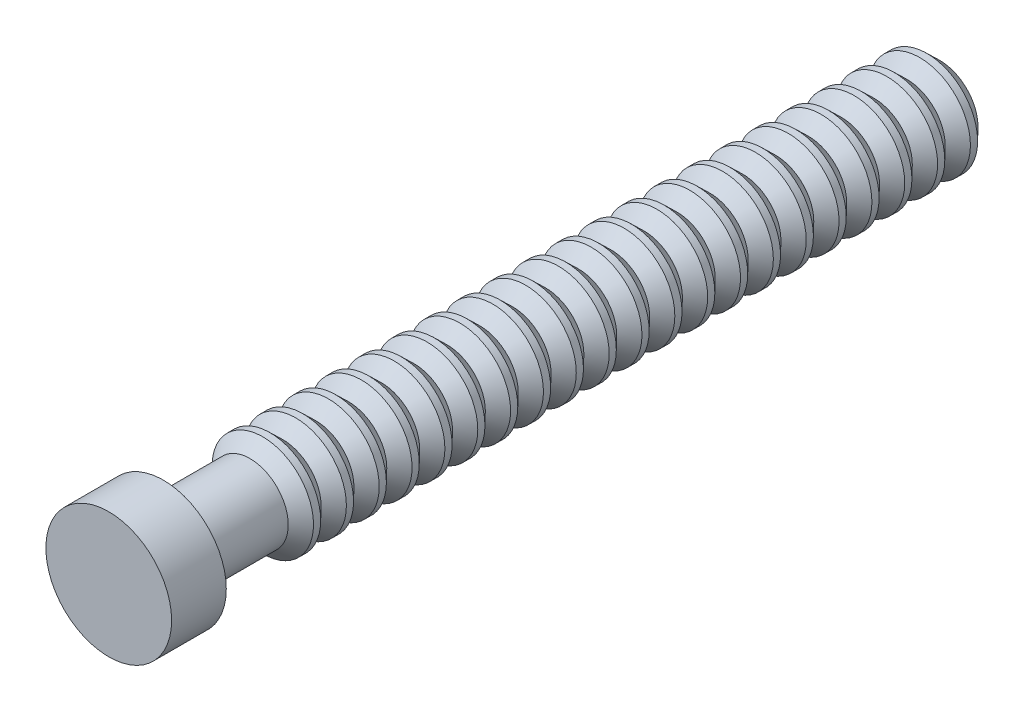
SolidWorks part; units mm, degrees
material "ASTM A36 Steel"
ref_plane "Front Plane" through (0, 0, 0) normal (0, 0, 1) x (1, 0, 0)
ref_plane "Top Plane" through (0, 0, 0) normal (0, 1, 0) x (1, 0, 0)
ref_plane "Right Plane" through (0, 0, 0) normal (1, 0, 0) x (0, 0, -1)
sketch "Sketch1" plane through (0, 0, 0) normal (0, 0, 1) x (1, 0, 0)
  circle A0 centre (0, 0) radius 7.3025
  dimension "D1" = 14.605
extrude "Boss-Extrude1" add sketch "Sketch1" along normal blind 6.35
sketch "Sketch2" plane through (0, 0, 0) normal (0, 0, 1) x (1, 0, 0)
  circle A0 centre (0, 0) radius 4.445
  dimension "D1" = 8.89
extrude "Boss-Extrude2" add sketch "Sketch2" against normal blind 90.17
sketch "Sketch5" plane through (0, 0, 0) normal (1, 0, 0) x (0, 0, -1)
  line L0 (90.17, 0) -> (99.2048, 0) construction
  line L1 (90.17, -4.445) -> (90.17, 4.445) construction
sketch "Sketch7" plane through (0, 0, 0) normal (1, 0, 0) x (0, 0, -1)
  line L0 (6.3474, 4.4475) -> (6.3449, 4.445)
  line L2 (86.3574, 4.4475) -> (84.8678, 5.8902)
  line L4 (86.36, 4.445) -> (84.8678, 5.8902)
  line L45 (84.8678, 5.8902) -> (84.0342, 5.8902)
  line L46 (84.0342, 5.8902) -> (82.5474, 4.4475)
  line L47 (82.5474, 4.4475) -> (81.0578, 5.8902)
  line L48 (90.17, 4.445) -> (88.6778, 5.8902)
  line L49 (88.6778, 5.8902) -> (87.8442, 5.8902)
  line L50 (87.8442, 5.8902) -> (86.3574, 4.4475)
  line L51 (82.5474, 4.4475) -> (81.0578, 5.8902)
  line L52 (90.17, 4.445) -> (0, 4.445) construction
  line L53 (81.0578, 5.8902) -> (80.2242, 5.8902)
  line L54 (6.3449, 4.445) -> (6.35, 4.445)
  line L55 (86.36, 4.445) -> (90.17, 4.445)
  line L56 (80.2242, 5.8902) -> (78.7374, 4.4475)
  line L57 (74.93, 4.445) -> (86.36, 4.445)
  line L59 (78.7374, 4.4475) -> (77.2478, 5.8902)
  line L62 (78.7374, 4.4475) -> (77.2478, 5.8902)
  line L65 (77.2478, 5.8902) -> (76.4142, 5.8902)
  line L68 (76.4142, 5.8902) -> (74.9274, 4.4475)
  line L71 (74.9274, 4.4475) -> (73.4378, 5.8902)
  line L74 (74.9274, 4.4475) -> (73.4378, 5.8902)
  line L77 (73.4378, 5.8902) -> (72.6042, 5.8902)
  line L80 (72.6042, 5.8902) -> (71.1174, 4.4475)
  line L83 (71.1174, 4.4475) -> (69.6278, 5.8902)
  line L86 (71.1174, 4.4475) -> (69.6278, 5.8902)
  line L89 (69.6278, 5.8902) -> (68.7942, 5.8902)
  line L92 (68.7942, 5.8902) -> (67.3074, 4.4475)
  line L95 (67.3074, 4.4475) -> (65.8178, 5.8902)
  line L98 (67.3074, 4.4475) -> (65.8178, 5.8902)
  line L101 (65.8178, 5.8902) -> (64.9842, 5.8902)
  line L104 (64.9842, 5.8902) -> (63.4974, 4.4475)
  line L107 (63.4974, 4.4475) -> (62.0078, 5.8902)
  line L110 (63.4974, 4.4475) -> (62.0078, 5.8902)
  line L111 (62.0078, 5.8902) -> (61.1742, 5.8902)
  line L113 (61.1742, 5.8902) -> (59.6874, 4.4475)
  line L114 (59.6874, 4.4475) -> (58.1978, 5.8902)
  line L115 (59.6874, 4.4475) -> (58.1978, 5.8902)
  line L116 (58.1978, 5.8902) -> (57.3642, 5.8902)
  line L117 (57.3642, 5.8902) -> (55.8774, 4.4475)
  line L118 (55.8774, 4.4475) -> (54.3878, 5.8902)
  line L119 (55.8774, 4.4475) -> (54.3878, 5.8902)
  line L120 (54.3878, 5.8902) -> (53.5542, 5.8902)
  line L121 (53.5542, 5.8902) -> (52.0674, 4.4475)
  line L122 (52.0674, 4.4475) -> (50.5778, 5.8902)
  line L123 (52.0674, 4.4475) -> (50.5778, 5.8902)
  line L124 (50.5778, 5.8902) -> (49.7442, 5.8902)
  line L125 (49.7442, 5.8902) -> (48.2574, 4.4475)
  line L126 (48.2574, 4.4475) -> (46.7678, 5.8902)
  line L127 (48.2574, 4.4475) -> (46.7678, 5.8902)
  line L128 (46.7678, 5.8902) -> (45.9342, 5.8902)
  line L129 (45.9342, 5.8902) -> (44.4474, 4.4475)
  line L130 (44.4474, 4.4475) -> (42.9578, 5.8902)
  line L131 (44.4474, 4.4475) -> (42.9578, 5.8902)
  line L132 (42.9578, 5.8902) -> (42.1242, 5.8902)
  line L133 (42.1242, 5.8902) -> (40.6374, 4.4475)
  line L134 (40.6374, 4.4475) -> (39.1478, 5.8902)
  line L135 (40.6374, 4.4475) -> (39.1478, 5.8902)
  line L136 (39.1478, 5.8902) -> (38.3142, 5.8902)
  line L137 (38.3142, 5.8902) -> (36.8274, 4.4475)
  line L138 (36.8274, 4.4475) -> (35.3378, 5.8902)
  line L139 (36.8274, 4.4475) -> (35.3378, 5.8902)
  line L140 (35.3378, 5.8902) -> (34.5042, 5.8902)
  line L141 (34.5042, 5.8902) -> (33.0174, 4.4475)
  line L142 (33.0174, 4.4475) -> (31.5278, 5.8902)
  line L143 (33.0174, 4.4475) -> (31.5278, 5.8902)
  line L144 (31.5278, 5.8902) -> (30.6942, 5.8902)
  line L145 (30.6942, 5.8902) -> (29.2074, 4.4475)
  line L146 (29.2074, 4.4475) -> (27.7178, 5.8902)
  line L147 (29.2074, 4.4475) -> (27.7178, 5.8902)
  line L148 (27.7178, 5.8902) -> (26.8842, 5.8902)
  line L149 (26.8842, 5.8902) -> (25.3974, 4.4475)
  line L150 (25.3974, 4.4475) -> (23.9078, 5.8902)
  line L151 (25.3974, 4.4475) -> (23.9078, 5.8902)
  line L152 (23.9078, 5.8902) -> (23.0742, 5.8902)
  line L153 (23.0742, 5.8902) -> (21.5874, 4.4475)
  line L154 (21.5874, 4.4475) -> (20.0978, 5.8902)
  line L155 (21.5874, 4.4475) -> (20.0978, 5.8902)
  line L156 (20.0978, 5.8902) -> (19.2642, 5.8902)
  line L157 (19.2642, 5.8902) -> (17.7774, 4.4475)
  line L158 (17.7774, 4.4475) -> (16.2878, 5.8902)
  line L159 (17.7774, 4.4475) -> (16.2878, 5.8902)
  line L160 (16.2878, 5.8902) -> (15.4542, 5.8902)
  line L161 (15.4542, 5.8902) -> (13.9674, 4.4475)
  line L162 (13.9674, 4.4475) -> (12.4778, 5.8902)
  line L163 (13.9674, 4.4475) -> (12.4778, 5.8902)
  line L164 (12.4778, 5.8902) -> (11.6442, 5.8902)
  line L165 (11.6442, 5.8902) -> (10.1574, 4.4475)
  line L166 (10.1574, 4.4475) -> (8.6678, 5.8902)
  line L167 (10.1574, 4.4475) -> (8.6678, 5.8902)
  line L168 (8.6678, 5.8902) -> (7.8342, 5.8902)
  line L169 (7.8342, 5.8902) -> (6.3474, 4.4475)
  line L170 (6.35, 4.445) -> (74.93, 4.445)
  line L171 (6.3474, 4.4475) -> (4.8578, 5.8902)
sketch "Sketch8" plane through (0, 0, 0) normal (1, 0, 0) x (0, 0, -1)
  line L5 (10.059, 4.445) -> (90.17, 4.445)
  line L112 (90.17, 4.445) -> (88.6778, 5.8902)
  line L113 (88.6778, 5.8902) -> (87.8442, 5.8902)
  line L114 (87.8442, 5.8902) -> (86.3574, 4.4475)
  line L115 (86.36, 4.445) -> (90.17, 4.445)
  line L116 (86.3574, 4.4475) -> (86.355, 4.445)
  line L120 (90.17, 4.445) -> (0, 4.445) construction
  line L127 (86.3499, 4.445) -> (86.36, 4.445)
  line L129 (86.3525, 4.4475) -> (86.355, 4.445)
  line L130 (84.8657, 5.8902) -> (86.3525, 4.4475)
  line L131 (84.0322, 5.8902) -> (84.8657, 5.8902)
  line L132 (82.5399, 4.445) -> (84.0322, 5.8902)
  line L133 (86.3499, 4.445) -> (78.7299, 4.445)
  line L134 (10.0564, 4.4475) -> (10.0539, 4.445)
  line L136 (80.2142, 5.8902) -> (78.7274, 4.4475)
  line L138 (81.0477, 5.8902) -> (80.2142, 5.8902)
  line L139 (82.5399, 4.445) -> (81.0477, 5.8902)
  line L140 (78.7274, 4.4475) -> (78.7249, 4.445)
  line L141 (78.7249, 4.445) -> (78.7299, 4.445)
  line L147 (76.4021, 5.8902) -> (77.2356, 5.8902)
  line L148 (74.9099, 4.445) -> (76.4021, 5.8902)
  line L149 (71.0999, 4.445) -> (74.9099, 4.445)
  line L150 (77.2356, 5.8902) -> (78.7224, 4.4475)
  line L153 (73.4176, 5.8902) -> (72.5841, 5.8902)
  line L154 (72.5841, 5.8902) -> (71.0973, 4.4475)
  line L155 (74.9099, 4.445) -> (73.4176, 5.8902)
  line L156 (71.0973, 4.4475) -> (71.0948, 4.445)
  line L161 (67.2798, 4.445) -> (68.772, 5.8902)
  line L162 (69.6055, 5.8902) -> (71.0923, 4.4475)
  line L164 (71.0923, 4.4475) -> (71.0948, 4.445)
  line L165 (68.772, 5.8902) -> (69.6055, 5.8902)
  line L169 (65.7875, 5.8902) -> (64.954, 5.8902)
  line L170 (64.954, 5.8902) -> (63.4672, 4.4475)
  line L171 (67.2798, 4.445) -> (65.7875, 5.8902)
  line L172 (63.4672, 4.4475) -> (63.4647, 4.445)
  line L176 (59.6496, 4.445) -> (61.1418, 5.8902)
  line L177 (61.1418, 5.8902) -> (61.9753, 5.8902)
  line L178 (61.9753, 5.8902) -> (63.4621, 4.4475)
  line L179 (63.4621, 4.4475) -> (63.4647, 4.445)
  line L181 (78.7224, 4.4475) -> (78.7249, 4.445)
  line L184 (57.3238, 5.8902) -> (55.837, 4.4475)
  line L185 (58.1573, 5.8902) -> (57.3238, 5.8902)
  line L186 (59.6496, 4.445) -> (58.1573, 5.8902)
  line L187 (55.837, 4.4475) -> (55.8345, 4.445)
  line L194 (55.832, 4.4475) -> (55.8345, 4.445)
  line L195 (52.0195, 4.445) -> (53.5117, 5.8902)
  line L196 (53.5117, 5.8902) -> (54.3452, 5.8902)
  line L197 (54.3452, 5.8902) -> (55.832, 4.4475)
  line L198 (32.9466, 4.4475) -> (32.9442, 4.445)
  line L199 (48.2069, 4.4475) -> (48.2044, 4.445)
  line L200 (49.6937, 5.8902) -> (48.2069, 4.4475)
  line L201 (50.5272, 5.8902) -> (49.6937, 5.8902)
  line L202 (52.0195, 4.445) -> (50.5272, 5.8902)
  line L203 (48.2044, 4.445) -> (48.2044, 4.46)
  line L204 (48.2018, 4.4475) -> (48.2044, 4.445)
  line L205 (44.3893, 4.445) -> (45.8815, 5.8902)
  line L206 (46.715, 5.8902) -> (48.2018, 4.4475)
  line L207 (45.8815, 5.8902) -> (46.715, 5.8902)
  line L209 (42.897, 5.8902) -> (42.0635, 5.8902)
  line L210 (40.5767, 4.4475) -> (40.5742, 4.445)
  line L211 (42.0635, 5.8902) -> (40.5767, 4.4475)
  line L212 (44.3893, 4.445) -> (42.897, 5.8902)
  line L213 (40.5718, 4.4475) -> (40.5742, 4.445)
  line L214 (36.7592, 4.445) -> (38.2514, 5.8902)
  line L215 (39.0849, 5.8902) -> (40.5718, 4.4475)
  line L216 (38.2514, 5.8902) -> (39.0849, 5.8902)
  line L217 (34.4334, 5.8902) -> (32.9466, 4.4475)
  line L218 (40.5692, 4.445) -> (36.7592, 4.445)
  line L219 (36.7592, 4.445) -> (35.2669, 5.8902)
  line L220 (35.2669, 5.8902) -> (34.4334, 5.8902)
  line L221 (32.9442, 4.445) -> (32.9391, 4.445)
  line L222 (32.9417, 4.4475) -> (32.9442, 4.445)
  line L223 (29.1291, 4.445) -> (30.6214, 5.8902)
  line L224 (30.6214, 5.8902) -> (31.4549, 5.8902)
  line L225 (31.4549, 5.8902) -> (32.9417, 4.4475)
  line L227 (25.3191, 4.445) -> (32.9391, 4.445)
  line L228 (29.1291, 4.445) -> (27.6369, 5.8902)
  line L229 (27.6369, 5.8902) -> (26.8034, 5.8902)
  line L230 (26.8034, 5.8902) -> (25.3166, 4.4475)
  line L231 (25.3166, 4.4475) -> (25.3141, 4.445)
  line L232 (25.3191, 4.445) -> (25.3091, 4.445)
  line L233 (25.3116, 4.4475) -> (25.3141, 4.445)
  line L234 (25.3091, 4.445) -> (17.6891, 4.445)
  line L235 (23.8248, 5.8902) -> (25.3116, 4.4475)
  line L236 (22.9913, 5.8902) -> (23.8248, 5.8902)
  line L237 (21.4991, 4.445) -> (22.9913, 5.8902)
  line L239 (21.4991, 4.445) -> (21.4991, 4.5673)
  line L241 (21.4991, 4.445) -> (20.0068, 5.8902)
  line L242 (20.0068, 5.8902) -> (19.1733, 5.8902)
  line L243 (19.1733, 5.8902) -> (17.6865, 4.4475)
  line L245 (17.6865, 4.4475) -> (17.684, 4.445)
  line L246 (17.679, 4.445) -> (17.6891, 4.445)
  line L247 (17.6815, 4.4475) -> (17.684, 4.445)
  line L248 (16.1947, 5.8902) -> (17.6815, 4.4475)
  line L249 (15.3612, 5.8902) -> (16.1947, 5.8902)
  line L250 (13.869, 4.445) -> (15.3612, 5.8902)
  line L251 (17.679, 4.445) -> (10.059, 4.445)
  line L253 (11.5432, 5.8902) -> (10.0564, 4.4475)
  line L254 (12.3767, 5.8902) -> (11.5432, 5.8902)
  line L255 (13.869, 4.445) -> (12.3767, 5.8902)
  line L256 (10.0539, 4.445) -> (10.059, 4.445)
revolve "Revolve2" add sketch "Sketch8" angle 360 about L0
